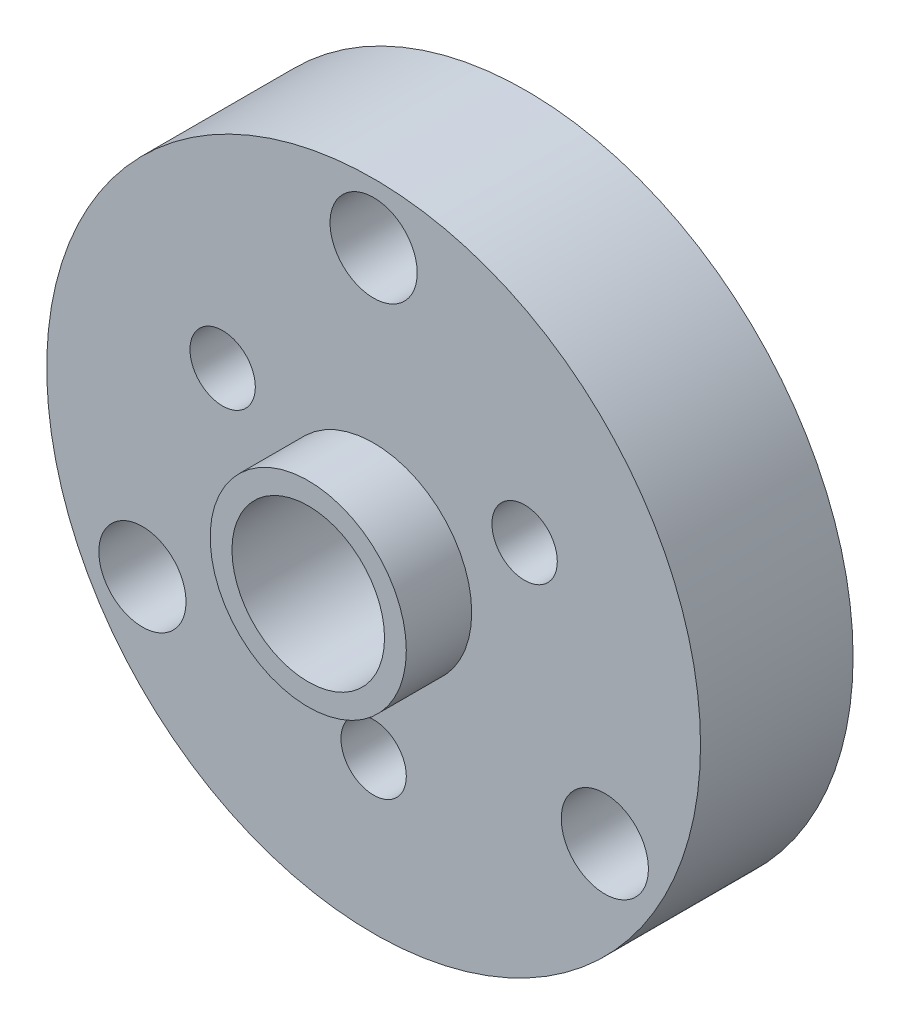
SolidWorks part; units mm, degrees
ref_plane "Plan de face" through (0, 0, 0) normal (0, 0, 1) x (1, 0, 0)
ref_plane "Plan de dessus" through (0, 0, 0) normal (0, 1, 0) x (1, 0, 0)
ref_plane "Plan de droite" through (0, 0, 0) normal (1, 0, 0) x (0, 0, -1)
sketch "Esquisse1" plane through (0, 0, 0) normal (0, 0, 1) x (1, 0, 0)
  circle A0 centre (0, 0) radius 15
  circle A1 centre (0, 0) radius 3.5
  circle A2 centre (10.6088, -6.125) radius 2
  circle A3 centre (0, 12.25) radius 2
  circle A4 centre (-10.6088, -6.125) radius 2
  circle A5 centre (-6.9282, 4) radius 1.5
  circle A6 centre (6.9282, 4) radius 1.5
  circle A7 centre (0, -8) radius 1.5
  dimension "D1" = 3
  dimension "D2" = 7
  dimension "D3" = 8
extrude "Extrusion1" add sketch "Esquisse1" along normal blind 7
sketch "Esquisse2" plane through (0, 0, 7) normal (0, 0, 1) x (1, 0, 0)
  circle A0 centre (0, 0) radius 3.5
  circle A1 centre (0, 0) radius 4.5
extrude "Extrusion2" add sketch "Esquisse2" along normal blind 3
sketch "Esquisse3" plane through (0, 0, 0) normal (0, 0, -1) x (-1, 0, 0)
  circle A0 centre (0, 0) radius 6
extrude "Extrusion3" cut sketch "Esquisse3" against normal blind 4
sketch "Esquisse4" plane through (0, 0, 4) normal (0, 0, -1) x (-1, 0, 0)
  circle A0 centre (0, 0) radius 5
  circle A1 centre (0, 0) radius 3.5
extrude "Extrusion4" cut sketch "Esquisse4" against normal blind 0.5
